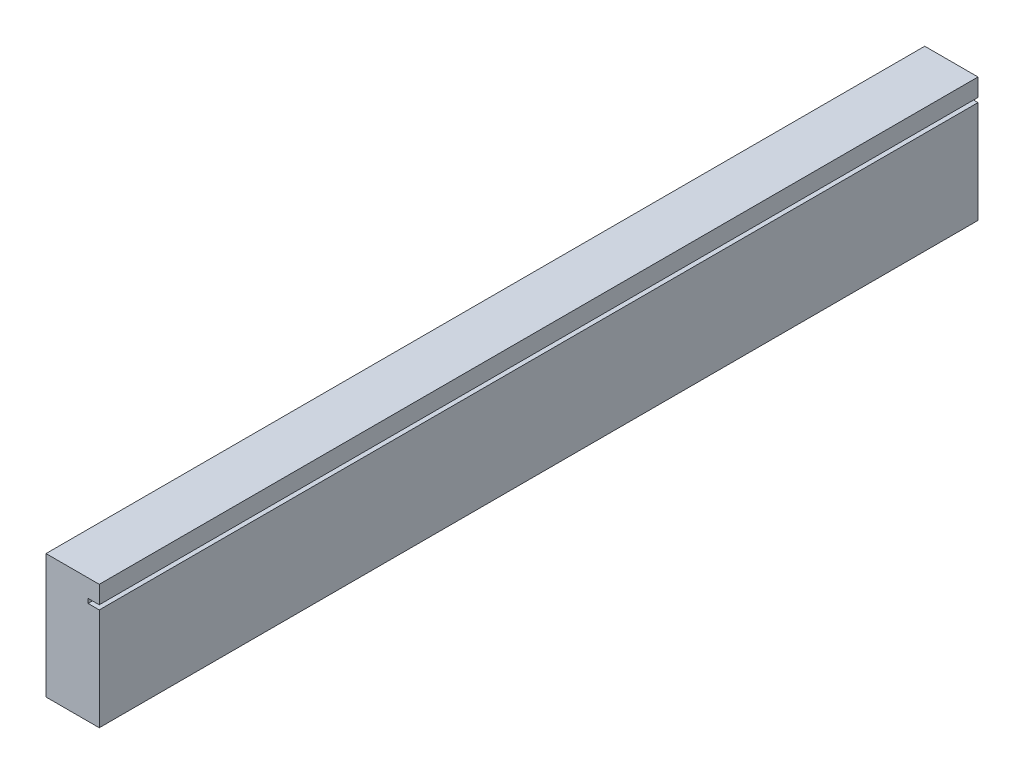
SolidWorks part; units mm, degrees
ref_plane "Front" through (0, 0, 0) normal (0, 0, 1) x (1, 0, 0)
ref_plane "Top" through (0, 0, 0) normal (0, 1, 0) x (1, 0, 0)
ref_plane "Right" through (0, 0, 0) normal (1, 0, 0) x (0, 0, -1)
sketch "Sketch1" plane through (0, 0, 0) normal (0, 0, 1) x (1, 0, 0)
  line L1 (-19.05, 44.45) -> (19.05, 44.45)
  line L2 (-19.05, 44.45) -> (-19.05, -44.45)
  line L3 (-19.05, -44.45) -> (19.05, -44.45)
  line L4 (19.05, 44.45) -> (19.05, -44.45)
  line L5 (-19.05, 44.45) -> (19.05, -44.45) construction
  line L6 (-19.05, -44.45) -> (19.05, 44.45) construction
  point P0 (0, 0)
  dimension "D1" = 38.1
  dimension "D2" = 88.9
extrude "Boss-Extrude1" add sketch "Sketch1" along normal mid plane 628.65
sketch "Sketch2" plane through (0, 0, 0) normal (0, 0, 1) x (1, 0, 0)
  line L0 (19.05, 31.75) -> (11.05, 31.75)
  line L1 (19.05, -44.45) -> (19.05, 44.45) construction
  line L2 (11.05, 31.75) -> (11.05, 28.575)
  line L3 (11.05, 28.575) -> (19.05, 28.575)
  line L4 (19.05, 28.575) -> (19.05, 31.75)
  line L5 (19.05, 44.45) -> (-19.05, 44.45) construction
  dimension "D1" = 3.175
  dimension "D2" = 8
  dimension "D3" = 12.7
extrude "Cut-Extrude1" cut sketch "Sketch2" against normal through all both and the other way through all
